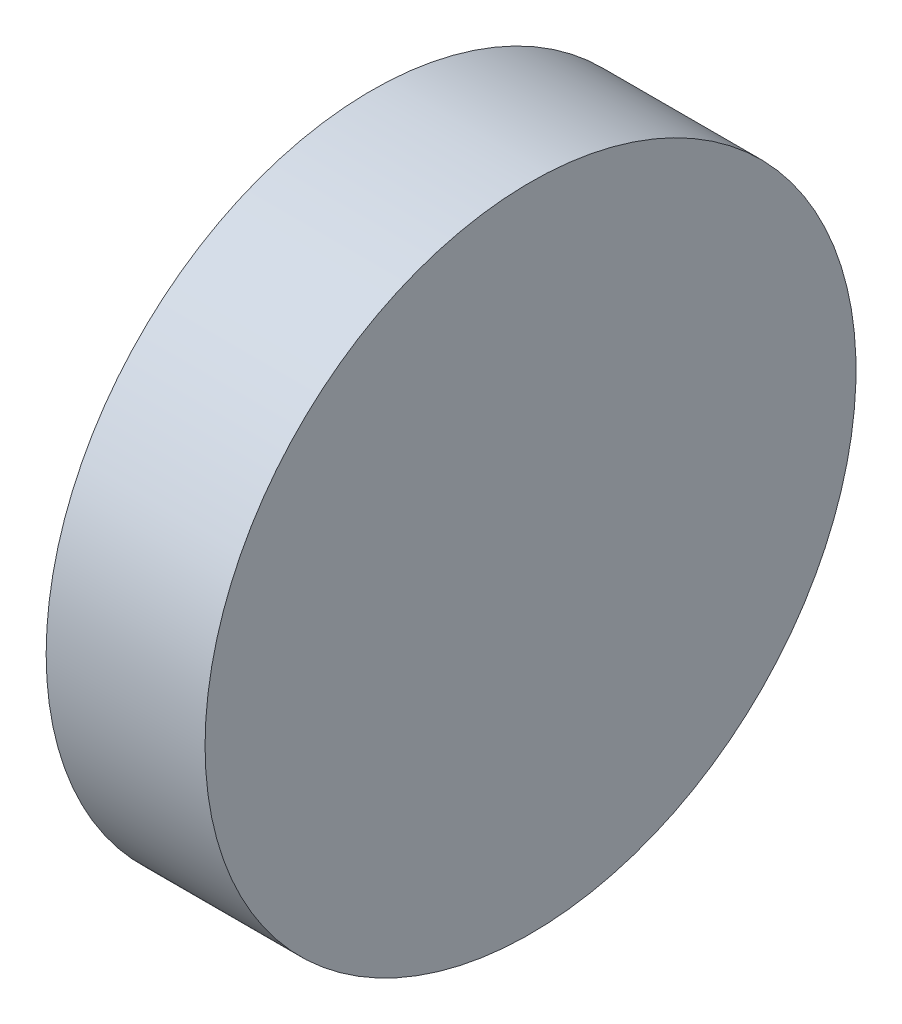
SolidWorks part; units mm, degrees
ref_plane "前视基准面" through (0, 0, 0) normal (0, 0, 1) x (1, 0, 0)
ref_plane "上视基准面" through (0, 0, 0) normal (0, 1, 0) x (1, 0, 0)
ref_plane "右视基准面" through (0, 0, 0) normal (1, 0, 0) x (0, 0, -1)
sketch "草图1" plane through (0, 0, 0) normal (0, 0, 1) x (1, 0, 0)
  line L0 (254.0008, 83.6432) -> (270.031, 83.6432) construction
  line L1 (259.7244, 83.6432) -> (259.7244, 89.9932)
  line L2 (262.8244, 83.6432) -> (262.8244, 89.9932)
  line L3 (259.7244, 83.6432) -> (262.8244, 83.6432)
  line L4 (259.7244, 89.9932) -> (262.8244, 89.9932)
  dimension "D1" = 6.35
  dimension "D2" = 3.1
revolve "旋转1" add sketch "草图1" angle 360 about L0
